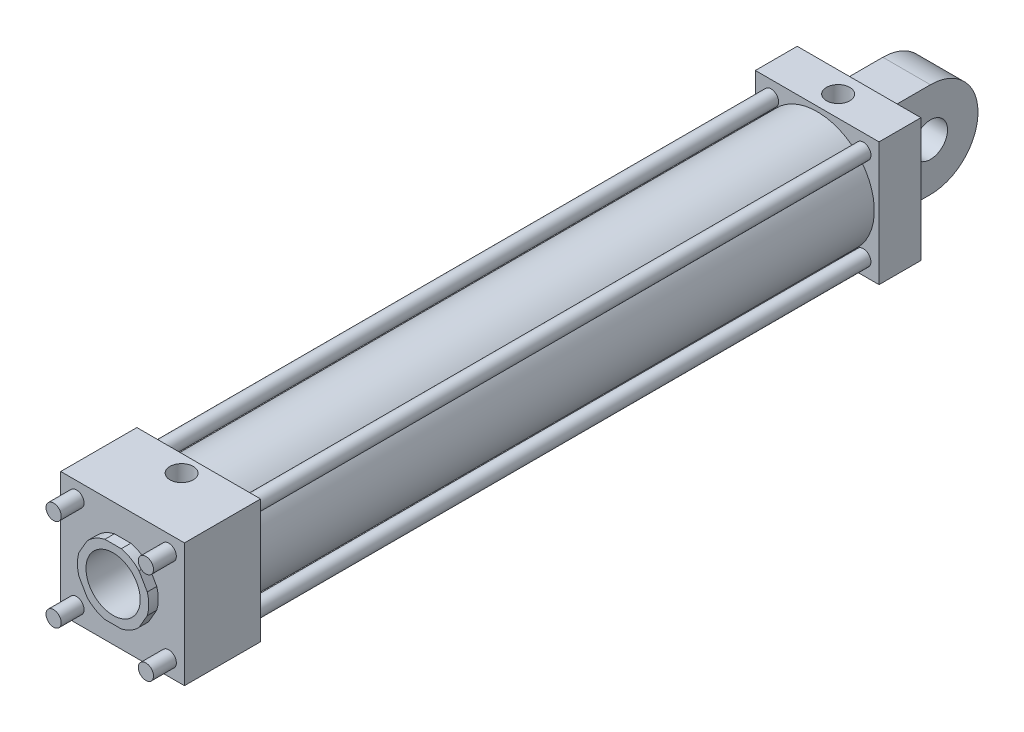
SolidWorks part; units mm, degrees
ref_plane "Plano frontal" through (0, 0, 0) normal (0, 0, 1) x (1, 0, 0)
ref_plane "Plano superior" through (0, 0, 0) normal (0, 1, 0) x (1, 0, 0)
ref_plane "Plano direito" through (0, 0, 0) normal (1, 0, 0) x (0, 0, -1)
sketch "Esboço1" plane through (0, 0, 0) normal (0, 0, 1) x (1, 0, 0)
  line L1 (-65, -65) -> (65, -65)
  line L2 (-65, -65) -> (-65, 65)
  line L3 (-65, 65) -> (65, 65)
  line L4 (65, -65) -> (65, 65)
  line L5 (-65, -65) -> (65, 65) construction
  line L6 (-65, 65) -> (65, -65) construction
  point P0 (0, 0)
  dimension "D1" = 130
  dimension "D2" = 130
extrude "Ressalto-extrusão1" add sketch "Esboço1" along normal blind 44
sketch "Esboço13" plane through (0, 0, 44) normal (0, 0, 1) x (1, 0, 0)
  circle A0 centre (0, 0) radius 45
  circle A1 centre (0, 0) radius 40
  dimension "D1" = 90
  dimension "D2" = 80
extrude "Ressalto-extrusão7" add sketch "Esboço13" along normal blind 10
sketch "Esboço2" plane through (0, 0, 44) normal (0, 0, 1) x (1, 0, 0)
  circle A0 centre (0, 0) radius 60
  circle A1 centre (0, 0) radius 50
  dimension "D1" = 120
  dimension "D2" = 100
extrude "Ressalto-extrusão2" add sketch "Esboço2" along normal blind 650
sketch "Esboço3" plane through (0, 0, 694) normal (0, 0, 1) x (1, 0, 0)
  line L1 (-65, -65) -> (65, -65)
  line L2 (-65, -65) -> (-65, 65)
  line L3 (-65, 65) -> (65, 65)
  line L4 (65, -65) -> (65, 65)
  line L5 (-65, -65) -> (65, 65) construction
  line L6 (-65, 65) -> (65, -65) construction
  point P0 (0, 0)
extrude "Ressalto-extrusão3" add sketch "Esboço3" along normal blind 80
sketch "Esboço4" plane through (0, 0, 44) normal (0, 0, 1) x (1, 0, 0)
  line L0 (-48.5, 0) -> (0, 0) construction
  line L1 (-48.5, -48.5) -> (48.5, -48.5) construction
  line L2 (-48.5, -48.5) -> (-48.5, 48.5) construction
  line L3 (-48.5, 48.5) -> (48.5, 48.5) construction
  line L4 (48.5, -48.5) -> (48.5, 48.5) construction
  line L5 (-48.5, -48.5) -> (48.5, 48.5) construction
  line L6 (-48.5, 48.5) -> (48.5, -48.5) construction
  line L7 (0, 0) -> (0, 48.5) construction
  circle A0 centre (-48.5, 48.5) radius 8
  circle A1 centre (-48.5, -48.5) radius 8
  circle A2 centre (48.5, -48.5) radius 8
  circle A3 centre (48.5, 48.5) radius 8
  point P0 (0, 0)
  dimension "D3" = 16
  dimension "D1" = 97
  dimension "D2" = 97
extrude "Ressalto-extrusão4" add sketch "Esboço4" along normal blind 754
sketch "Esboço5" plane through (0, 0, 774) normal (0, 0, 1) x (1, 0, 0)
  circle A0 centre (0, 0) radius 37.5
  dimension "D1" = 75
extrude "Ressalto-extrusão5" add sketch "Esboço5" along normal blind 10
sketch "Esboço6" plane through (0, 0, 784) normal (0, 0, 1) x (1, 0, 0)
  line L0 (0, 0) -> (42.1466, 0) construction
  line L1 (42.1466, 0) -> (21.0733, 36.5)
  line L2 (21.0733, 36.5) -> (-21.0733, 36.5)
  line L3 (-21.0733, 36.5) -> (-42.1466, 0)
  line L4 (-42.1466, 0) -> (-21.0733, -36.5)
  line L5 (-21.0733, -36.5) -> (21.0733, -36.5)
  line L6 (21.0733, -36.5) -> (42.1466, 0)
  circle A0 centre (0, 0) radius 36.5 construction
  circle A1 centre (0, 0) radius 37.5
  circle M8 centre (0, 0) radius 37.5
  dimension "D1" = 73
extrude "Corte-extrusão1" cut sketch "Esboço6" against normal blind 10 contours L3 M8 | L2 M8 | L1 M8 | L4 M8 | L5 M8 | L6 M8
sketch "Esboço7" plane through (0, 0, 784) normal (0, 0, 1) x (1, 0, 0)
  circle A0 centre (0, 0) radius 28.5
  dimension "D1" = 57
extrude "Corte-extrusão2" cut sketch "Esboço7" against normal blind 280
sketch "Esboço8" plane through (0, 0, 0) normal (0, 0, -1) x (-1, 0, 0)
  line L1 (-25, -50) -> (25, -50)
  line L2 (-25, -50) -> (-25, 50)
  line L3 (-25, 50) -> (25, 50)
  line L4 (25, -50) -> (25, 50)
  line L5 (-25, -50) -> (25, 50) construction
  line L6 (-25, 50) -> (25, -50) construction
  point P0 (0, 0)
  dimension "D1" = 100
  dimension "D2" = 50
extrude "Ressalto-extrusão6" add sketch "Esboço8" along normal blind 100
sketch "Esboço9" plane through (-25, 0, 0) normal (-1, 0, 0) x (0, 0, 1)
  line L0 (0, 0) -> (-100, 0) construction
  line L1 (-100, -50) -> (-100, 50) construction
  line L3 (0, -50) -> (-100, -50)
  line L4 (0, -50) -> (0, 50)
  line L5 (0, 50) -> (-100, 50)
  line L6 (-100, -50) -> (-100, 50)
  line L7 (0, -50) -> (-100, 50) construction
  line L8 (0, 50) -> (-100, -50) construction
  circle A0 centre (-50, 0) radius 50
  circle A1 centre (-50, 0) radius 18
  line M8 (-100, 50) -> (-100, -50)
  line M9 (-100, -50) -> (0, -50)
  dimension "D1" = 36
extrude "Corte-extrusão3" cut sketch "Esboço9" against normal through all contours A0 L5 M8 | A0 L6 M9 | A1
sketch "Esboço10" plane through (0, 65, 0) normal (0, 1, 0) x (1, 0, 0)
  line L0 (0, 0) -> (0, -44) construction
  line L1 (-60, -44) -> (60, -44) construction
  circle A0 centre (0, -22) radius 12.25
  dimension "D1" = 24.5
extrude "Corte-extrusão4" cut sketch "Esboço10" against normal blind 65
sketch "Esboço11" plane through (0, 65, 0) normal (0, 1, 0) x (1, 0, 0)
  line L0 (0, -22) -> (0, -712) construction
  circle A0 centre (0, -712) radius 12.25
  dimension "D2" = 24.5
  dimension "D1" = 690
extrude "Corte-extrusão5" cut sketch "Esboço11" against normal blind 65
sketch "Esboço12" plane through (0, 0, 44) normal (0, 0, 1) x (1, 0, 0)
  circle A0 centre (0, 0) radius 40
  dimension "D1" = 80
extrude "Corte-extrusão6" cut sketch "Esboço12" against normal blind 22
sketch "Esboço14" plane through (0, 0, 694) normal (0, 0, -1) x (-1, 0, 0)
  circle A0 centre (0, 0) radius 45
  circle A1 centre (0, 0) radius 40
  dimension "D1" = 90
  dimension "D2" = 80
extrude "Ressalto-extrusão8" add sketch "Esboço14" along normal blind 10
